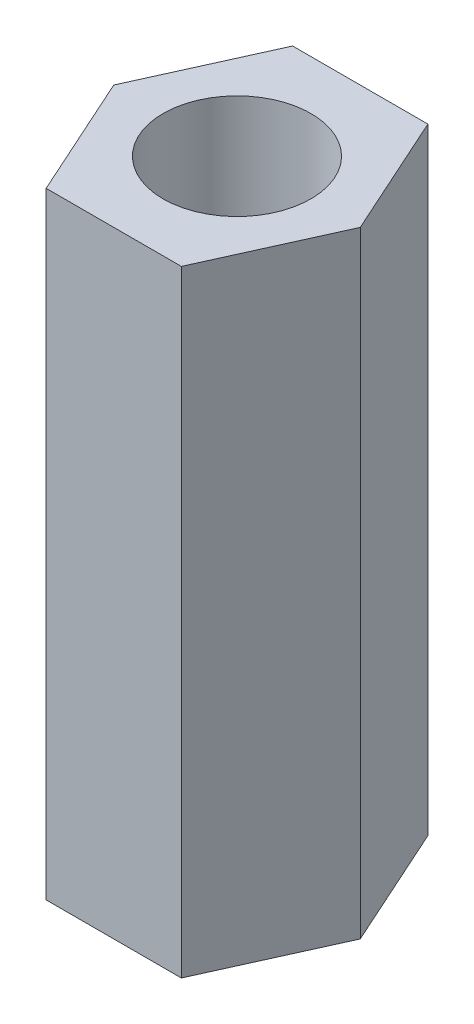
SolidWorks part; units mm, degrees
material "Malleable Cast Iron"
ref_plane "Front Plane" through (0, 0, 0) normal (0, 0, 1) x (1, 0, 0)
ref_plane "Top Plane" through (0, 0, 0) normal (0, 1, 0) x (1, 0, 0)
ref_plane "Right Plane" through (0, 0, 0) normal (1, 0, 0) x (0, 0, -1)
sketch "Sketch1" plane through (0, 0, 0) normal (0, 1, 0) x (1, 0, 0)
  line L0 (-5, 0) -> (-2.7429, 5)
  line L1 (-2.7429, 5) -> (2.7429, 5)
  line L2 (2.7429, 5) -> (5, 0)
  line L3 (5, 0) -> (2.7429, -5)
  line L4 (2.7429, -5) -> (-2.7429, -5)
  line L5 (-2.7429, -5) -> (-5, 0)
  line L6 (-2.7429, -5) -> (2.7429, 5) construction
  circle A0 centre (0, 0) radius 3
  point P6 (0, 0)
  dimension "D1" = 6
  dimension "D2" = 10
  dimension "D3" = 10
extrude "Extrude1" add sketch "Sketch1" along normal blind 25
